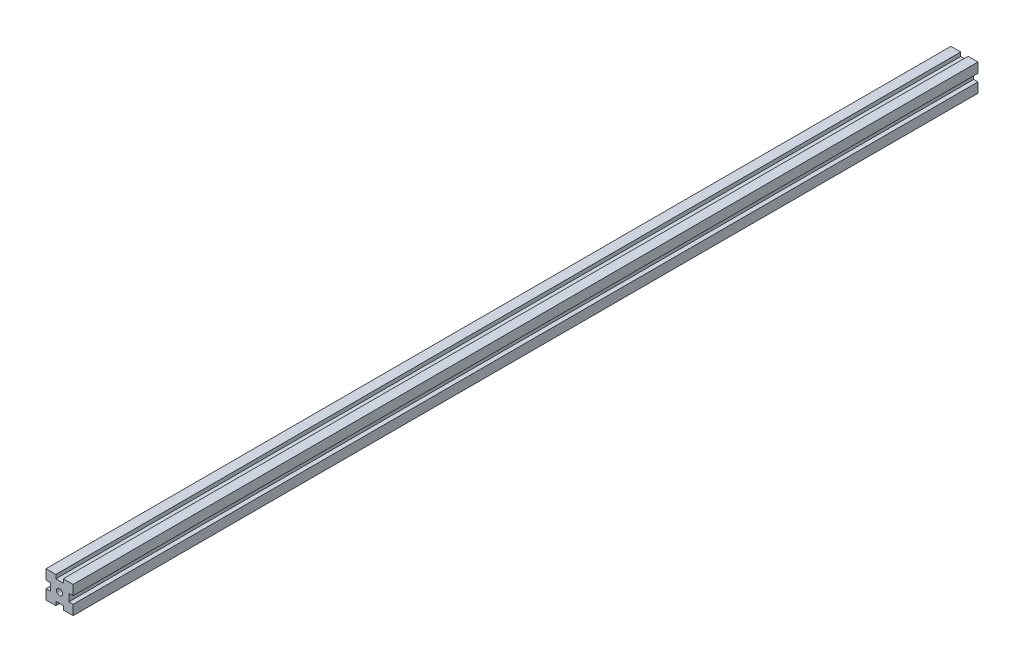
SolidWorks part; units mm, degrees
material "1060-H12 棒材(SS)"
ref_plane "前视基准面" through (0, 0, 0) normal (0, 0, 1) x (1, 0, 0)
ref_plane "上视基准面" through (0, 0, 0) normal (0, 1, 0) x (1, 0, 0)
ref_plane "右视基准面" through (0, 0, 0) normal (1, 0, 0) x (0, 0, -1)
other "Configuration Table"
sketch "草图1" plane through (0, 0, 0) normal (0, 0, 1) x (1, 0, 0)
  line L0 (3.3505, 10.2134) -> (3.3505, -11.2443) construction
  line L1 (-11.6495, 14.4845) -> (-0.7495, 14.4845)
  line L2 (-11.6495, 14.4845) -> (-11.6495, 3.5845)
  line L3 (-11.6495, -15.5155) -> (-0.7495, -15.5155)
  line L4 (18.3505, 14.4845) -> (18.3505, 3.5845)
  line L5 (-11.6495, 3.5845) -> (-6.893, 3.5845)
  line L7 (-11.6495, -4.6155) -> (-6.893, -4.6155)
  line L8 (-6.893, 3.5845) -> (-6.893, -4.6155)
  line L10 (-0.7495, 14.4845) -> (-0.7495, 10.2134)
  line L11 (-0.7495, 10.2134) -> (7.4505, 10.2134)
  line L12 (7.4505, 14.4845) -> (7.4505, 10.2134)
  line L13 (-6.893, -0.5155) -> (13.594, -0.5155) construction
  line L14 (18.3505, -4.6155) -> (13.594, -4.6155)
  line L15 (13.594, 3.5845) -> (13.594, -4.6155)
  line L16 (18.3505, 3.5845) -> (13.594, 3.5845)
  line L18 (-0.7495, -11.2443) -> (7.4505, -11.2443)
  line L19 (7.4505, -15.5155) -> (7.4505, -11.2443)
  line L21 (-0.7495, -15.5155) -> (-0.7495, -11.2443)
  line L22 (-11.6495, -4.6155) -> (-11.6495, -15.5155)
  line L23 (7.4505, 14.4845) -> (18.3505, 14.4845)
  line L24 (18.3505, -4.6155) -> (18.3505, -15.5155)
  line L25 (7.4505, -15.5155) -> (18.3505, -15.5155)
  circle A0 centre (3.3505, -0.5155) radius 3.4
  dimension "D5" = 6.8
  dimension "D1" = 30
  dimension "D2" = 30
  dimension "D3" = 8.2
  dimension "D4" = 8.2
extrude "凸台-拉伸1" add sketch "草图1" along normal blind 1000
